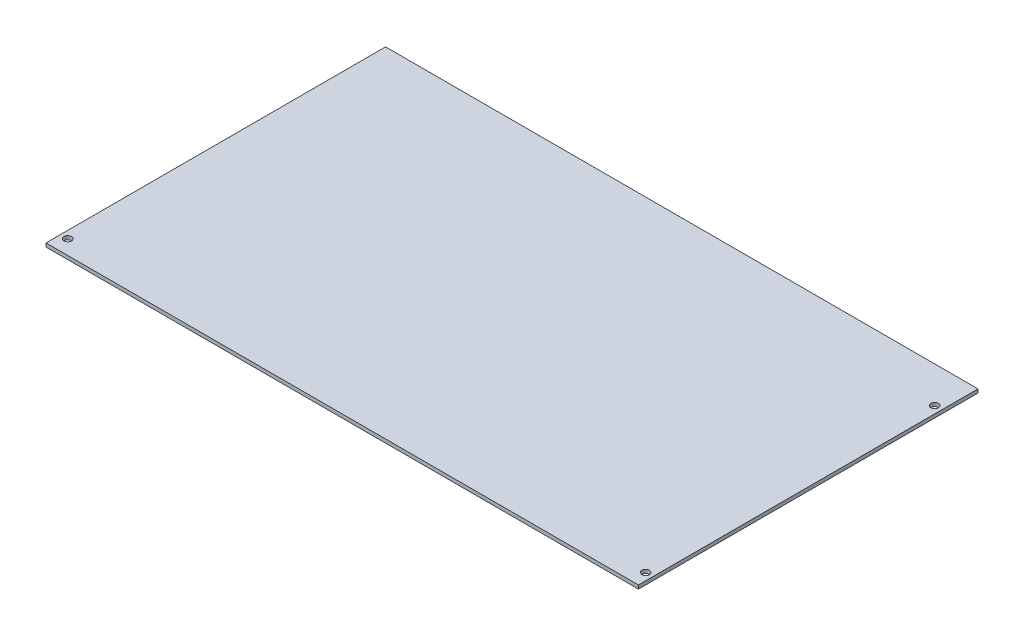
SolidWorks part; units mm, degrees
ref_plane "Front" through (0, 0, 0) normal (0, 0, 1) x (1, 0, 0)
ref_plane "Top" through (0, 0, 0) normal (0, 1, 0) x (1, 0, 0)
ref_plane "Right" through (0, 0, 0) normal (1, 0, 0) x (0, 0, -1)
sketch "Sketch1" plane through (0, 0, 0) normal (0, 1, 0) x (1, 0, 0)
  line L1 (0, 0) -> (520.7, 0)
  line L2 (0, 0) -> (0, 298.45)
  line L3 (0, 298.45) -> (520.7, 298.45)
  line L4 (520.7, 0) -> (520.7, 298.45)
  line L5 (0, 0) -> (520.7, 298.45) construction
  line L6 (0, 298.45) -> (520.7, 0) construction
  point P4 (260.35, 149.225)
  dimension "D1" = 298.45
  dimension "D2" = 520.7
extrude "Boss-Extrude1" add sketch "Sketch1" along normal blind 3.175
sketch "Sketch2" plane through (0, 0, 0) normal (0, -1, 0) x (1, 0, 0)
  circle A0 centre (6.35, -12.7) radius 3.3528 construction
  circle A1 centre (6.35, -12.7) radius 3.3528
  circle A2 centre (514.35, -12.7) radius 3.3528 construction
  circle A3 centre (514.35, -12.7) radius 3.3528
  circle A4 centre (514.35, -266.7) radius 3.3528 construction
  circle A5 centre (514.35, -266.7) radius 3.3528
extrude "Cut-Extrude1" cut sketch "Sketch2" against normal up to next
